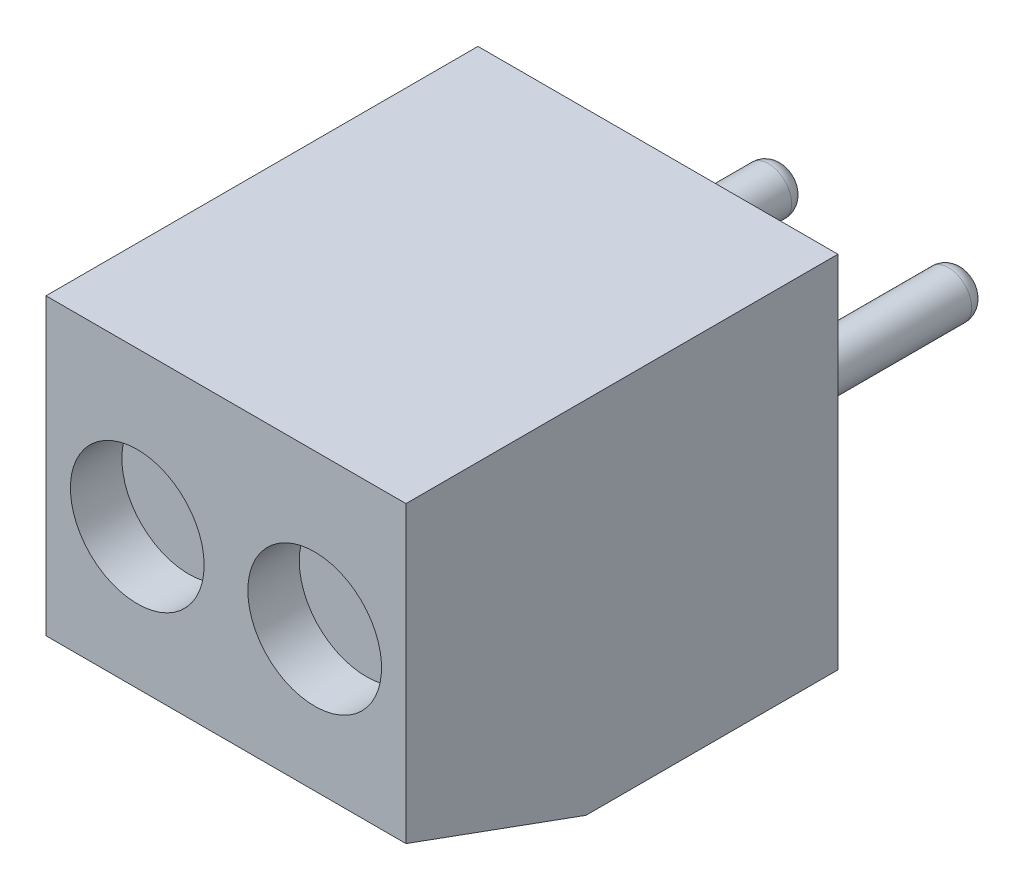
SolidWorks part; units mm, degrees
ref_plane "Front" through (0, 0, 0) normal (0, 0, 1) x (1, 0, 0)
ref_plane "Top" through (0, 0, 0) normal (0, 1, 0) x (1, 0, 0)
ref_plane "Right" through (0, 0, 0) normal (1, 0, 0) x (0, 0, -1)
sketch "Sketch1" plane through (0, 0, 0) normal (0, 0, 1) x (1, 0, 0)
  line L1 (-3.5, -3.5) -> (3.5, -3.5)
  line L2 (-3.5, -3.5) -> (-3.5, 3.5)
  line L3 (-3.5, 3.5) -> (3.5, 3.5)
  line L4 (3.5, -3.5) -> (3.5, 3.5)
  line L5 (-3.5, -3.5) -> (3.5, 3.5) construction
  line L6 (-3.5, 3.5) -> (3.5, -3.5) construction
  point P0 (0, 0)
  dimension "D1" = 7
  dimension "D2" = 7
extrude "Boss-Extrude1" add sketch "Sketch1" along normal blind 8.4
chamfer "Chamfer1" distance 3.5 angle 20 1 edges at (0, -3.5, 8.4)
sketch "Sketch2" plane through (0, -3.5, 0) normal (0, -1, 0) x (1, 0, 0)
  line L0 (0, 0) -> (0, 3.7734) construction
  line L1 (-3.5, 0) -> (3.5, 0) construction
  line L2 (0.3, 4.7) -> (0.3, 0.5)
  line L3 (-3.15, 4.7) -> (-0.3, 4.7)
  line L4 (-3.15, 4.7) -> (-3.15, 0.5)
  line L5 (-3.15, 0.5) -> (-0.3, 0.5)
  line L6 (-0.3, 4.7) -> (-0.3, 0.5)
  line L7 (3.15, 0.5) -> (0.3, 0.5)
  line L8 (3.15, 4.7) -> (3.15, 0.5)
  line L9 (3.15, 4.7) -> (0.3, 4.7)
  line L10 (-3.5, 4.9) -> (-3.5, 0) construction
  dimension "D1" = 0.6
  dimension "D2" = 0.35
  dimension "D3" = 0.5
  dimension "D4" = 4.2
extrude "Cut-Extrude1" cut sketch "Sketch2" against normal blind 1.8
sketch "Sketch3" plane through (0, -1.7, 0) normal (0, -1, 0) x (1, 0, 0)
  line L0 (-3.15, 4.7) -> (-0.3, 0.5) construction
  line L1 (0, 0) -> (0, 2.1417) construction
  circle A0 centre (-1.725, 2.6) radius 1
  circle A1 centre (1.725, 2.6) radius 1
  dimension "D1" = 2
extrude "Cut-Extrude2" cut sketch "Sketch3" against normal offset from surface (4.2 mm away) 1 up to face at (0, 3.5, 4.2)
sketch "Sketch4" plane through (0, 0, 8.4) normal (0, 0, 1) x (1, 0, 0)
  line L0 (-1.725, 2.5) -> (-1.725, 0.5) construction
  line L1 (-2.725, 2.5) -> (-0.725, 2.5) construction
  line L2 (3.5, 3.5) -> (-3.5, 3.5) construction
  line L3 (0, 0) -> (0, 2.0441) construction
  circle A0 centre (-1.725, 0.5) radius 1.3
  circle A1 centre (1.725, 0.5) radius 1.3
  dimension "D1" = 2.6
  dimension "D2" = 3
extrude "Cut-Extrude3" cut sketch "Sketch4" against normal blind 1
sketch "Sketch5" plane through (0, 0, 0) normal (0, 0, -1) x (-1, 0, 0)
  line L0 (0, 0) -> (0, 1.5375) construction
  circle A0 centre (-1.75, 0) radius 0.45
  circle A1 centre (1.75, 0) radius 0.45
  dimension "D1" = 0.9
  dimension "D2" = 3.5
extrude "Boss-Extrude2" add sketch "Sketch5" along normal blind 4.2
fillet "Fillet1" radius 0.3 2 edges at (1.3, 0, -4.2) (-1.3, 0, -4.2)
